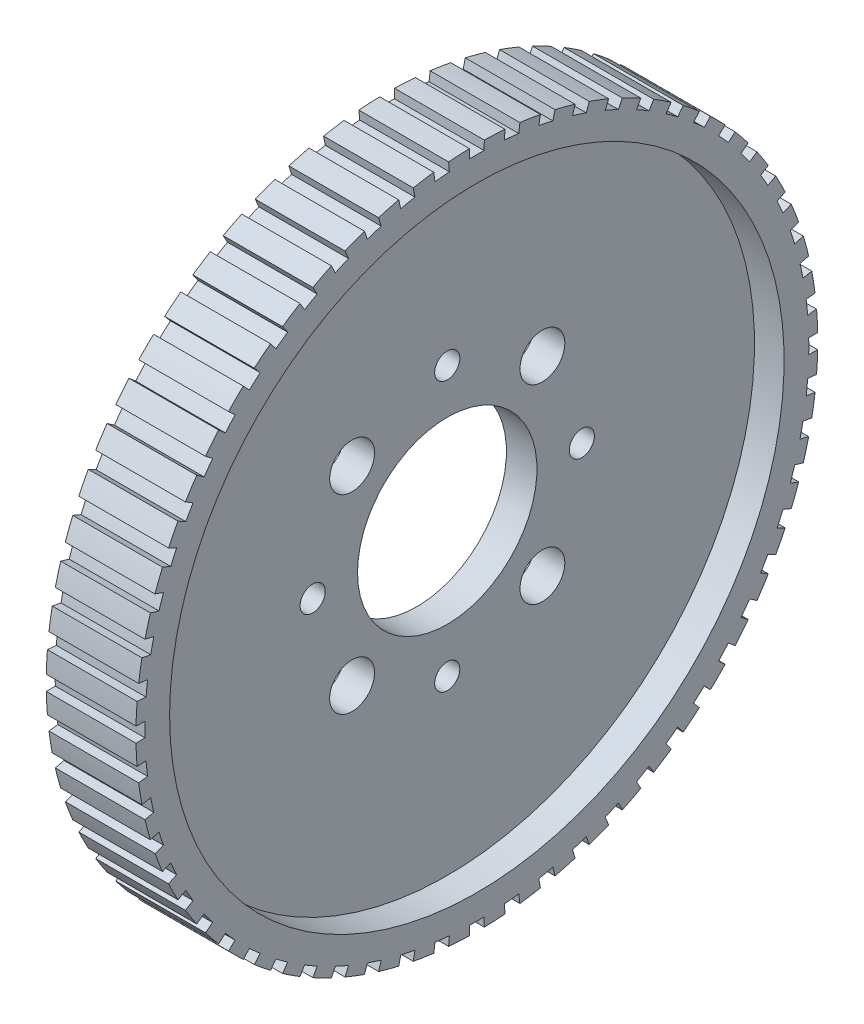
SolidWorks part; units mm, degrees
ref_plane "Front Plane" through (0, 0, 0) normal (0, 0, 1) x (1, 0, 0)
ref_plane "Top Plane" through (0, 0, 0) normal (0, 1, 0) x (1, 0, 0)
ref_plane "Right Plane" through (0, 0, 0) normal (1, 0, 0) x (0, 0, -1)
sketch "Sketch1" plane through (0, 0, 0) normal (0, 0, 1) x (1, 0, 0)
  line L0 (0, 0) -> (22.6465, 0) construction
  line L1 (-2.159, 12.7) -> (2.159, 12.7)
  line L2 (2.159, 12.7) -> (2.159, 43.4975)
  line L3 (2.159, 43.4975) -> (6.35, 43.4975)
  line L4 (6.35, 43.4975) -> (6.35, 48.26)
  line L5 (6.35, 48.26) -> (-6.35, 48.26)
  line L6 (-6.35, 48.26) -> (-6.35, 43.4975)
  line L7 (-6.35, 43.4975) -> (-2.159, 43.4975)
  line L8 (-2.159, 43.4975) -> (-2.159, 12.7)
  dimension "D1" = 4.318
  dimension "D2" = 48.26
  dimension "D3" = 12.7
  dimension "D4" = 43.4975
  dimension "D5" = 6.35
  dimension "D6" = 6.35
  dimension "D7" = 4.191
revolve "Revolve1" add sketch "Sketch1" angle 360 about L0
sketch "Sketch2" plane through (2.159, 0, 0) normal (1, 0, 0) x (0, 0, -1)
  circle A0 centre (0, 0) radius 19.05 construction
  circle A1 centre (0, 19.05) radius 1.778
  circle A2 centre (0, 0) radius 19.05 construction
  circle A3 centre (19.05, 0) radius 1.778
  circle A4 centre (0, 0) radius 19.05 construction
  circle A5 centre (0, -19.05) radius 1.778
  circle A6 centre (0, 0) radius 19.05 construction
  circle A7 centre (-19.05, 0) radius 1.778
  circle A8 centre (-13.4704, 13.4704) radius 3.175
  circle A9 centre (0, 0) radius 19.05 construction
  circle A10 centre (13.4704, 13.4704) radius 3.175
  circle A11 centre (0, 0) radius 19.05 construction
  circle A12 centre (13.4704, -13.4704) radius 3.175
  circle A13 centre (0, 0) radius 19.05 construction
  circle A14 centre (-13.4704, -13.4704) radius 3.175
  point P17 (0, 0)
  point P29 (0, 0)
  dimension "D1" = 38.1
  dimension "D2" = 3.556
  dimension "D4" = 6.35
  dimension "D5" = 45
  dimension "D3" = 4
  dimension "D6" = 4
extrude "Cut-Extrude1" cut sketch "Sketch2" against normal through all
sketch "Sketch3" plane through (6.35, 0, 0) normal (1, 0, 0) x (0, 0, -1)
  line L0 (-1.0251, 46.9788) -> (-1.0805, 49.5188)
  line L1 (0, 0) -> (0, 72.6164) construction
  line L2 (1.0251, 46.9788) -> (1.0805, 49.5188)
  line L3 (-1.0805, 49.5188) -> (1.0805, 49.5188)
  line L4 (4.1015, 49.3605) -> (6.2507, 49.1346)
  line L5 (3.8912, 46.8286) -> (4.1015, 49.3605)
  line L6 (5.9301, 46.6143) -> (6.2507, 49.1346)
  line L7 (9.2386, 48.6614) -> (11.3524, 48.2121)
  line L8 (8.7648, 46.1653) -> (9.2386, 48.6614)
  line L9 (10.7701, 45.7391) -> (11.3524, 48.2121)
  line L10 (14.2745, 47.4291) -> (16.3298, 46.7613)
  line L11 (13.5423, 44.9963) -> (14.2745, 47.4291)
  line L12 (15.4922, 44.3627) -> (16.3298, 46.7613)
  line L13 (19.154, 45.6772) -> (21.1282, 44.7982)
  line L14 (18.1715, 43.3342) -> (19.154, 45.6772)
  line L15 (20.0445, 42.5003) -> (21.1282, 44.7982)
  line L16 (23.8237, 43.4248) -> (25.6952, 42.3443)
  line L17 (22.6017, 41.1974) -> (23.8237, 43.4248)
  line L18 (24.3772, 40.1723) -> (25.6952, 42.3443)
  line L19 (28.2323, 40.6967) -> (29.9806, 39.4265)
  line L20 (26.7841, 38.6092) -> (28.2323, 40.6967)
  line L21 (28.4428, 37.4041) -> (29.9806, 39.4265)
  line L22 (32.3316, 37.5227) -> (33.9375, 36.0767)
  line L23 (30.6732, 35.598) -> (32.3316, 37.5227)
  line L24 (32.1967, 34.2262) -> (33.9375, 36.0767)
  line L25 (36.0767, 33.9375) -> (37.5227, 32.3316)
  line L26 (34.2262, 32.1967) -> (36.0767, 33.9375)
  line L27 (35.598, 30.6732) -> (37.5227, 32.3316)
  line L28 (39.4265, 29.9806) -> (40.6967, 28.2323)
  line L29 (37.4041, 28.4428) -> (39.4265, 29.9806)
  line L30 (38.6092, 26.7841) -> (40.6967, 28.2323)
  line L31 (42.3443, 25.6952) -> (43.4248, 23.8237)
  line L32 (40.1723, 24.3772) -> (42.3443, 25.6952)
  line L33 (41.1974, 22.6017) -> (43.4248, 23.8237)
  line L34 (44.7982, 21.1282) -> (45.6772, 19.154)
  line L35 (42.5003, 20.0445) -> (44.7982, 21.1282)
  line L36 (43.3342, 18.1715) -> (45.6772, 19.154)
  line L37 (46.7613, 16.3298) -> (47.4291, 14.2745)
  line L38 (44.3627, 15.4922) -> (46.7613, 16.3298)
  line L39 (44.9963, 13.5423) -> (47.4291, 14.2745)
  line L40 (48.2121, 11.3524) -> (48.6614, 9.2386)
  line L41 (45.7391, 10.7701) -> (48.2121, 11.3524)
  line L42 (46.1653, 8.7648) -> (48.6614, 9.2386)
  line L43 (49.1346, 6.2507) -> (49.3605, 4.1015)
  line L44 (46.6143, 5.9301) -> (49.1346, 6.2507)
  line L45 (46.8286, 3.8912) -> (49.3605, 4.1015)
  line L46 (49.5188, 1.0805) -> (49.5188, -1.0805)
  line L47 (46.9788, 1.0251) -> (49.5188, 1.0805)
  line L48 (46.9788, -1.0251) -> (49.5188, -1.0805)
  line L49 (49.3605, -4.1015) -> (49.1346, -6.2507)
  line L50 (46.8286, -3.8912) -> (49.3605, -4.1015)
  line L51 (46.6143, -5.9301) -> (49.1346, -6.2507)
  line L52 (48.6614, -9.2386) -> (48.2121, -11.3524)
  line L53 (46.1653, -8.7648) -> (48.6614, -9.2386)
  line L54 (45.7391, -10.7701) -> (48.2121, -11.3524)
  line L55 (47.4291, -14.2745) -> (46.7613, -16.3298)
  line L56 (44.9963, -13.5423) -> (47.4291, -14.2745)
  line L57 (44.3627, -15.4922) -> (46.7613, -16.3298)
  line L58 (45.6772, -19.154) -> (44.7982, -21.1282)
  line L59 (43.3342, -18.1715) -> (45.6772, -19.154)
  line L60 (42.5003, -20.0445) -> (44.7982, -21.1282)
  line L61 (43.4248, -23.8237) -> (42.3443, -25.6952)
  line L62 (41.1974, -22.6017) -> (43.4248, -23.8237)
  line L63 (40.1723, -24.3772) -> (42.3443, -25.6952)
  line L64 (40.6967, -28.2323) -> (39.4265, -29.9806)
  line L65 (38.6092, -26.7841) -> (40.6967, -28.2323)
  line L66 (37.4041, -28.4428) -> (39.4265, -29.9806)
  line L67 (37.5227, -32.3316) -> (36.0767, -33.9375)
  line L68 (35.598, -30.6732) -> (37.5227, -32.3316)
  line L69 (34.2262, -32.1967) -> (36.0767, -33.9375)
  line L70 (33.9375, -36.0767) -> (32.3316, -37.5227)
  line L71 (32.1967, -34.2262) -> (33.9375, -36.0767)
  line L72 (30.6732, -35.598) -> (32.3316, -37.5227)
  line L73 (29.9806, -39.4265) -> (28.2323, -40.6967)
  line L74 (28.4428, -37.4041) -> (29.9806, -39.4265)
  line L75 (26.7841, -38.6092) -> (28.2323, -40.6967)
  line L76 (25.6952, -42.3443) -> (23.8237, -43.4248)
  line L77 (24.3772, -40.1723) -> (25.6952, -42.3443)
  line L78 (22.6017, -41.1974) -> (23.8237, -43.4248)
  line L79 (21.1282, -44.7982) -> (19.154, -45.6772)
  line L80 (20.0445, -42.5003) -> (21.1282, -44.7982)
  line L81 (18.1715, -43.3342) -> (19.154, -45.6772)
  line L82 (16.3298, -46.7613) -> (14.2745, -47.4291)
  line L83 (15.4922, -44.3627) -> (16.3298, -46.7613)
  line L84 (13.5423, -44.9963) -> (14.2745, -47.4291)
  line L85 (11.3524, -48.2121) -> (9.2386, -48.6614)
  line L86 (10.7701, -45.7391) -> (11.3524, -48.2121)
  line L87 (8.7648, -46.1653) -> (9.2386, -48.6614)
  line L88 (6.2507, -49.1346) -> (4.1015, -49.3605)
  line L89 (5.9301, -46.6143) -> (6.2507, -49.1346)
  line L90 (3.8912, -46.8286) -> (4.1015, -49.3605)
  line L91 (1.0805, -49.5188) -> (-1.0805, -49.5188)
  line L92 (1.0251, -46.9788) -> (1.0805, -49.5188)
  line L93 (-1.0251, -46.9788) -> (-1.0805, -49.5188)
  line L94 (-4.1015, -49.3605) -> (-6.2507, -49.1346)
  line L95 (-3.8912, -46.8286) -> (-4.1015, -49.3605)
  line L96 (-5.9301, -46.6143) -> (-6.2507, -49.1346)
  line L97 (-9.2386, -48.6614) -> (-11.3524, -48.2121)
  line L98 (-8.7648, -46.1653) -> (-9.2386, -48.6614)
  line L99 (-10.7701, -45.7391) -> (-11.3524, -48.2121)
  line L100 (-14.2745, -47.4291) -> (-16.3298, -46.7613)
  line L101 (-13.5423, -44.9963) -> (-14.2745, -47.4291)
  line L102 (-15.4922, -44.3627) -> (-16.3298, -46.7613)
  line L103 (-19.154, -45.6772) -> (-21.1282, -44.7982)
  line L104 (-18.1715, -43.3342) -> (-19.154, -45.6772)
  line L105 (-20.0445, -42.5003) -> (-21.1282, -44.7982)
  line L106 (-23.8237, -43.4248) -> (-25.6952, -42.3443)
  line L107 (-22.6017, -41.1974) -> (-23.8237, -43.4248)
  line L108 (-24.3772, -40.1723) -> (-25.6952, -42.3443)
  line L109 (-28.2323, -40.6967) -> (-29.9806, -39.4265)
  line L110 (-26.7841, -38.6092) -> (-28.2323, -40.6967)
  line L111 (-28.4428, -37.4041) -> (-29.9806, -39.4265)
  line L112 (-32.3316, -37.5227) -> (-33.9375, -36.0767)
  line L113 (-30.6732, -35.598) -> (-32.3316, -37.5227)
  line L114 (-32.1967, -34.2262) -> (-33.9375, -36.0767)
  line L115 (-36.0767, -33.9375) -> (-37.5227, -32.3316)
  line L116 (-34.2262, -32.1967) -> (-36.0767, -33.9375)
  line L117 (-35.598, -30.6732) -> (-37.5227, -32.3316)
  line L118 (-39.4265, -29.9806) -> (-40.6967, -28.2323)
  line L119 (-37.4041, -28.4428) -> (-39.4265, -29.9806)
  line L120 (-38.6092, -26.7841) -> (-40.6967, -28.2323)
  line L121 (-42.3443, -25.6952) -> (-43.4248, -23.8237)
  line L122 (-40.1723, -24.3772) -> (-42.3443, -25.6952)
  line L123 (-41.1974, -22.6017) -> (-43.4248, -23.8237)
  line L124 (-44.7982, -21.1282) -> (-45.6772, -19.154)
  line L125 (-42.5003, -20.0445) -> (-44.7982, -21.1282)
  line L126 (-43.3342, -18.1715) -> (-45.6772, -19.154)
  line L127 (-46.7613, -16.3298) -> (-47.4291, -14.2745)
  line L128 (-44.3627, -15.4922) -> (-46.7613, -16.3298)
  line L129 (-44.9963, -13.5423) -> (-47.4291, -14.2745)
  line L130 (-48.2121, -11.3524) -> (-48.6614, -9.2386)
  line L131 (-45.7391, -10.7701) -> (-48.2121, -11.3524)
  line L132 (-46.1653, -8.7648) -> (-48.6614, -9.2386)
  line L133 (-49.1346, -6.2507) -> (-49.3605, -4.1015)
  line L134 (-46.6143, -5.9301) -> (-49.1346, -6.2507)
  line L135 (-46.8286, -3.8912) -> (-49.3605, -4.1015)
  line L136 (-49.5188, -1.0805) -> (-49.5188, 1.0805)
  line L137 (-46.9788, -1.0251) -> (-49.5188, -1.0805)
  line L138 (-46.9788, 1.0251) -> (-49.5188, 1.0805)
  line L139 (-49.3605, 4.1015) -> (-49.1346, 6.2507)
  line L140 (-46.8286, 3.8912) -> (-49.3605, 4.1015)
  line L141 (-46.6143, 5.9301) -> (-49.1346, 6.2507)
  line L142 (-48.6614, 9.2386) -> (-48.2121, 11.3524)
  line L143 (-46.1653, 8.7648) -> (-48.6614, 9.2386)
  line L144 (-45.7391, 10.7701) -> (-48.2121, 11.3524)
  line L145 (-47.4291, 14.2745) -> (-46.7613, 16.3298)
  line L146 (-44.9963, 13.5423) -> (-47.4291, 14.2745)
  line L147 (-44.3627, 15.4922) -> (-46.7613, 16.3298)
  line L148 (-45.6772, 19.154) -> (-44.7982, 21.1282)
  line L149 (-43.3342, 18.1715) -> (-45.6772, 19.154)
  line L150 (-42.5003, 20.0445) -> (-44.7982, 21.1282)
  line L151 (-43.4248, 23.8237) -> (-42.3443, 25.6952)
  line L152 (-41.1974, 22.6017) -> (-43.4248, 23.8237)
  line L153 (-40.1723, 24.3772) -> (-42.3443, 25.6952)
  line L154 (-40.6967, 28.2323) -> (-39.4265, 29.9806)
  line L155 (-38.6092, 26.7841) -> (-40.6967, 28.2323)
  line L156 (-37.4041, 28.4428) -> (-39.4265, 29.9806)
  line L157 (-37.5227, 32.3316) -> (-36.0767, 33.9375)
  line L158 (-35.598, 30.6732) -> (-37.5227, 32.3316)
  line L159 (-34.2262, 32.1967) -> (-36.0767, 33.9375)
  line L160 (-33.9375, 36.0767) -> (-32.3316, 37.5227)
  line L161 (-32.1967, 34.2262) -> (-33.9375, 36.0767)
  line L162 (-30.6732, 35.598) -> (-32.3316, 37.5227)
  line L163 (-29.9806, 39.4265) -> (-28.2323, 40.6967)
  line L164 (-28.4428, 37.4041) -> (-29.9806, 39.4265)
  line L165 (-26.7841, 38.6092) -> (-28.2323, 40.6967)
  line L166 (-25.6952, 42.3443) -> (-23.8237, 43.4248)
  line L167 (-24.3772, 40.1723) -> (-25.6952, 42.3443)
  line L168 (-22.6017, 41.1974) -> (-23.8237, 43.4248)
  line L169 (-21.1282, 44.7982) -> (-19.154, 45.6772)
  line L170 (-20.0445, 42.5003) -> (-21.1282, 44.7982)
  line L171 (-18.1715, 43.3342) -> (-19.154, 45.6772)
  line L172 (-16.3298, 46.7613) -> (-14.2745, 47.4291)
  line L173 (-15.4922, 44.3627) -> (-16.3298, 46.7613)
  line L174 (-13.5423, 44.9963) -> (-14.2745, 47.4291)
  line L175 (-11.3524, 48.2121) -> (-9.2386, 48.6614)
  line L176 (-10.7701, 45.7391) -> (-11.3524, 48.2121)
  line L177 (-8.7648, 46.1653) -> (-9.2386, 48.6614)
  line L178 (-6.2507, 49.1346) -> (-4.1015, 49.3605)
  line L179 (-5.9301, 46.6143) -> (-6.2507, 49.1346)
  line L180 (-3.8912, 46.8286) -> (-4.1015, 49.3605)
  arc A0 (1.0251, 46.9788) -> (-1.0251, 46.9788) centre (0, 0) ccw
  arc A1 (5.9301, 46.6143) -> (3.8912, 46.8286) centre (0, 0) ccw
  arc A2 (10.7701, 45.7391) -> (8.7648, 46.1653) centre (0, 0) ccw
  arc A3 (15.4922, 44.3627) -> (13.5423, 44.9963) centre (0, 0) ccw
  arc A4 (20.0445, 42.5003) -> (18.1715, 43.3342) centre (0, 0) ccw
  arc A5 (24.3772, 40.1723) -> (22.6017, 41.1974) centre (0, 0) ccw
  arc A6 (28.4428, 37.4041) -> (26.7841, 38.6092) centre (0, 0) ccw
  arc A7 (32.1967, 34.2262) -> (30.6732, 35.598) centre (0, 0) ccw
  arc A8 (35.598, 30.6732) -> (34.2262, 32.1967) centre (0, 0) ccw
  arc A9 (38.6092, 26.7841) -> (37.4041, 28.4428) centre (0, 0) ccw
  arc A10 (41.1974, 22.6017) -> (40.1723, 24.3772) centre (0, 0) ccw
  arc A11 (43.3342, 18.1715) -> (42.5003, 20.0445) centre (0, 0) ccw
  arc A12 (44.9963, 13.5423) -> (44.3627, 15.4922) centre (0, 0) ccw
  arc A13 (46.1653, 8.7648) -> (45.7391, 10.7701) centre (0, 0) ccw
  arc A14 (46.8286, 3.8912) -> (46.6143, 5.9301) centre (0, 0) ccw
  arc A15 (46.9788, -1.0251) -> (46.9788, 1.0251) centre (0, 0) ccw
  arc A16 (46.6143, -5.9301) -> (46.8286, -3.8912) centre (0, 0) ccw
  arc A17 (45.7391, -10.7701) -> (46.1653, -8.7648) centre (0, 0) ccw
  arc A18 (44.3627, -15.4922) -> (44.9963, -13.5423) centre (0, 0) ccw
  arc A19 (42.5003, -20.0445) -> (43.3342, -18.1715) centre (0, 0) ccw
  arc A20 (40.1723, -24.3772) -> (41.1974, -22.6017) centre (0, 0) ccw
  arc A21 (37.4041, -28.4428) -> (38.6092, -26.7841) centre (0, 0) ccw
  arc A22 (34.2262, -32.1967) -> (35.598, -30.6732) centre (0, 0) ccw
  arc A23 (30.6732, -35.598) -> (32.1967, -34.2262) centre (0, 0) ccw
  arc A24 (26.7841, -38.6092) -> (28.4428, -37.4041) centre (0, 0) ccw
  arc A25 (22.6017, -41.1974) -> (24.3772, -40.1723) centre (0, 0) ccw
  arc A26 (18.1715, -43.3342) -> (20.0445, -42.5003) centre (0, 0) ccw
  arc A27 (13.5423, -44.9963) -> (15.4922, -44.3627) centre (0, 0) ccw
  arc A28 (8.7648, -46.1653) -> (10.7701, -45.7391) centre (0, 0) ccw
  arc A29 (3.8912, -46.8286) -> (5.9301, -46.6143) centre (0, 0) ccw
  arc A30 (-1.0251, -46.9788) -> (1.0251, -46.9788) centre (0, 0) ccw
  arc A31 (-5.9301, -46.6143) -> (-3.8912, -46.8286) centre (0, 0) ccw
  arc A32 (-10.7701, -45.7391) -> (-8.7648, -46.1653) centre (0, 0) ccw
  arc A33 (-15.4922, -44.3627) -> (-13.5423, -44.9963) centre (0, 0) ccw
  arc A34 (-20.0445, -42.5003) -> (-18.1715, -43.3342) centre (0, 0) ccw
  arc A35 (-24.3772, -40.1723) -> (-22.6017, -41.1974) centre (0, 0) ccw
  arc A36 (-28.4428, -37.4041) -> (-26.7841, -38.6092) centre (0, 0) ccw
  arc A37 (-32.1967, -34.2262) -> (-30.6732, -35.598) centre (0, 0) ccw
  arc A38 (-35.598, -30.6732) -> (-34.2262, -32.1967) centre (0, 0) ccw
  arc A39 (-38.6092, -26.7841) -> (-37.4041, -28.4428) centre (0, 0) ccw
  arc A40 (-41.1974, -22.6017) -> (-40.1723, -24.3772) centre (0, 0) ccw
  arc A41 (-43.3342, -18.1715) -> (-42.5003, -20.0445) centre (0, 0) ccw
  arc A42 (-44.9963, -13.5423) -> (-44.3627, -15.4922) centre (0, 0) ccw
  arc A43 (-46.1653, -8.7648) -> (-45.7391, -10.7701) centre (0, 0) ccw
  arc A44 (-46.8286, -3.8912) -> (-46.6143, -5.9301) centre (0, 0) ccw
  arc A45 (-46.9788, 1.0251) -> (-46.9788, -1.0251) centre (0, 0) ccw
  arc A46 (-46.6143, 5.9301) -> (-46.8286, 3.8912) centre (0, 0) ccw
  arc A47 (-45.7391, 10.7701) -> (-46.1653, 8.7648) centre (0, 0) ccw
  arc A48 (-44.3627, 15.4922) -> (-44.9963, 13.5423) centre (0, 0) ccw
  arc A49 (-42.5003, 20.0445) -> (-43.3342, 18.1715) centre (0, 0) ccw
  arc A50 (-40.1723, 24.3772) -> (-41.1974, 22.6017) centre (0, 0) ccw
  arc A51 (-37.4041, 28.4428) -> (-38.6092, 26.7841) centre (0, 0) ccw
  arc A52 (-34.2262, 32.1967) -> (-35.598, 30.6732) centre (0, 0) ccw
  arc A53 (-30.6732, 35.598) -> (-32.1967, 34.2262) centre (0, 0) ccw
  arc A54 (-26.7841, 38.6092) -> (-28.4428, 37.4041) centre (0, 0) ccw
  arc A55 (-22.6017, 41.1974) -> (-24.3772, 40.1723) centre (0, 0) ccw
  arc A56 (-18.1715, 43.3342) -> (-20.0445, 42.5003) centre (0, 0) ccw
  arc A57 (-13.5423, 44.9963) -> (-15.4922, 44.3627) centre (0, 0) ccw
  arc A58 (-8.7648, 46.1653) -> (-10.7701, 45.7391) centre (0, 0) ccw
  arc A59 (-3.8912, 46.8286) -> (-5.9301, 46.6143) centre (0, 0) ccw
  point P245 (0, 0)
  dimension "D1" = 93.98
  dimension "D2" = 2.54
  dimension "D3" = 2.54
  dimension "D4" = 1.25
  dimension "D5" = 1.25
  dimension "D6" = 60
extrude "Cut-Extrude2" cut sketch "Sketch3" against normal through all
